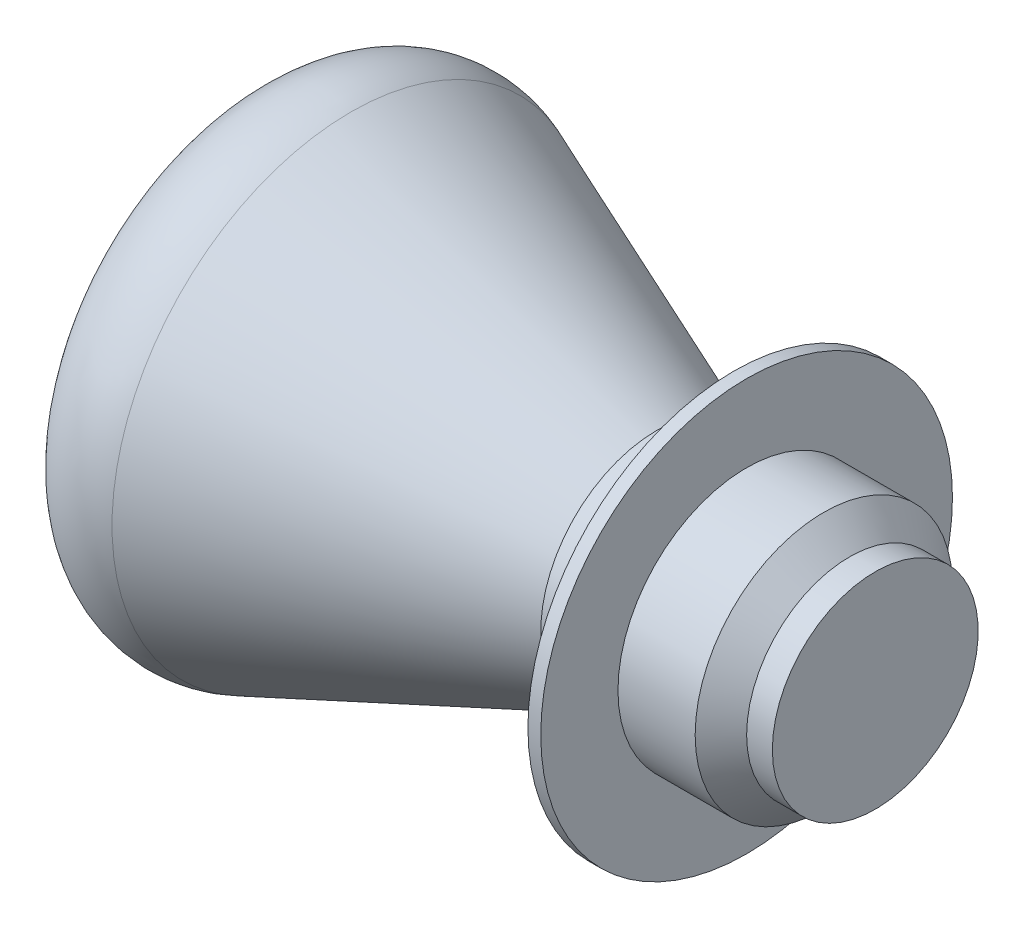
SolidWorks part; units mm, degrees
ref_plane "Front Plane" through (0, 0, 0) normal (0, 0, 1) x (1, 0, 0)
ref_plane "Top Plane" through (0, 0, 0) normal (0, 1, 0) x (1, 0, 0)
ref_plane "Right Plane" through (0, 0, 0) normal (1, 0, 0) x (0, 0, -1)
sketch "Sketch1" plane through (0, 0, 0) normal (0, 0, 1) x (1, 0, 0)
  line L0 (0, 4.5) -> (0, 0)
  line L1 (0, 0) -> (5.5, 0)
  line L2 (5.5, 0) -> (5.5, 4)
  line L3 (5.5, 4) -> (4.5, 4)
  line L4 (4.5, 4) -> (3.5, 5)
  line L5 (3.5, 5) -> (0.5, 5)
  line L6 (0.5, 5) -> (0.5, 8)
  line L7 (0.5, 8) -> (0, 8)
  line L8 (0, 8) -> (0, 5)
  line L9 (0, 5) -> (-2, 5)
  line L10 (-2, 5) -> (-2, 4.5)
  line L11 (-2, 4.5) -> (0, 4.5)
  point P12 (0.25, 8)
  dimension "D1" = 5.5
  dimension "D2" = 5
  dimension "D3" = 1
  dimension "D4" = 1
  dimension "D5" = 1
  dimension "D6" = 3
  dimension "D7" = 0.5
  dimension "D8" = 3
  dimension "D9" = 2
revolve "Revolve1" add sketch "Sketch1" angle 360 about L1
sketch "Sketch2" plane through (0, 0, 0) normal (0, 0, 1) x (1, 0, 0)
  line L0 (0, 0) -> (-17.231, 0) construction
  line L1 (0, 0) -> (0, 4.5)
  line L2 (0, 4.5) -> (-3, 4.5)
  line L3 (-3, 4.5) -> (-14.8796, 9.2829)
  line L4 (0, 0) -> (-19.8584, 0)
  line L5 (0, 8) -> (0, -8) construction
  arc A0 (-18.8972, 7.2788) -> (-19.8584, 0) centre (8.1816, 0) ccw
  arc A1 (-14.8796, 9.2829) -> (-18.8972, 7.2788) centre (-16, 6.5) ccw
  point P9 (-22.3517, 0)
  point P14 (-21.6604, 0)
  point P15 (-2.701, 2.1254)
  point P16 (-19.6761, 0)
  point P17 (-3.2697, 0)
  point P18 (-3.2697, 0)
  point P19 (-3, 0.9766)
  point P20 (-3, 0.9028)
  point P21 (-7.7697, -5.1864)
  point P22 (-3.3633, -15.1175)
  dimension "D1" = 3
  dimension "D4" = 28.04
  dimension "D2" = 16
  dimension "D3" = 2
  dimension "D5" = 3
revolve "Revolve2" add sketch "Sketch2" angle 360 about L4
